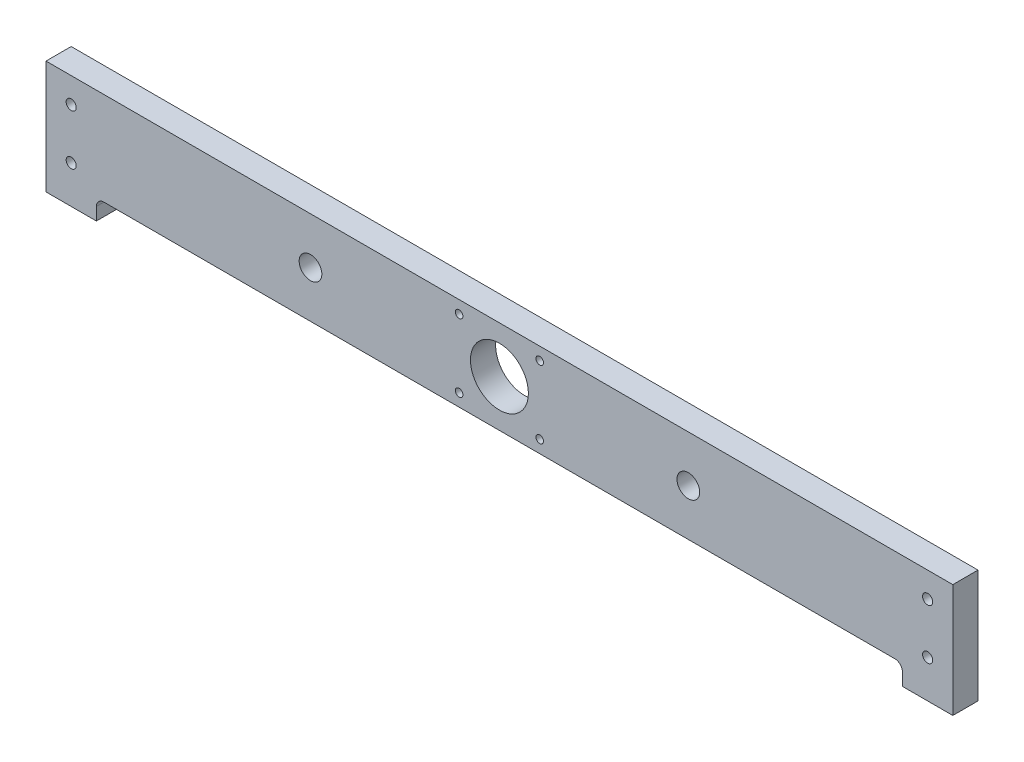
SolidWorks part; units mm, degrees
ref_plane "Front Plane" through (0, 0, 0) normal (0, 0, 1) x (1, 0, 0)
ref_plane "Top Plane" through (0, 0, 0) normal (0, 1, 0) x (1, 0, 0)
ref_plane "Right Plane" through (0, 0, 0) normal (1, 0, 0) x (0, 0, -1)
sketch "Sketch1" plane through (0, 0, 0) normal (0, 0, 1) x (1, 0, 0)
  line L0 (0, 0) -> (360, 0)
  line L1 (360, 0) -> (360, -45)
  line L2 (360, -45) -> (340, -45)
  line L3 (340, -45) -> (340, -40)
  line L4 (0, 0) -> (0, -45)
  line L5 (0, -45) -> (20, -45)
  line L6 (20, -45) -> (20, -40)
  line L7 (23, -37) -> (337, -37)
  arc A0 (23, -37) -> (20, -40) centre (23, -40) ccw
  arc A1 (340, -40) -> (337, -37) centre (337, -40) ccw
  circle A2 centre (350, -10) radius 2
  circle A3 centre (350, -30) radius 2
  circle A4 centre (10, -10) radius 2
  circle A5 centre (10, -30.0045) radius 2
  circle A6 centre (180, -18.5) radius 11.5
  circle A7 centre (255, -18.5) radius 4.5
  circle A8 centre (105, -18.5) radius 4.5
  circle A9 centre (164, -5) radius 1.5
  circle A10 centre (196, -5) radius 1.5
  circle A11 centre (196, -32) radius 1.5
  circle A12 centre (164, -32) radius 1.5
  point P11 (20, -37)
  point P29 (180, 0)
  point P37 (0, 0)
  point P38 (0, 0)
  dimension "D6" = 3
  dimension "D7" = 3
  dimension "D13" = 4
  dimension "D14" = 4
  dimension "D15" = 4
  dimension "D16" = 4
  dimension "D21" = 23
  dimension "D23" = 9
  dimension "D24" = 9
  dimension "D27" = 3
  dimension "D28" = 3
  dimension "D29" = 3
  dimension "D30" = 3
  dimension "D1" = 360
  dimension "D2" = 45
  dimension "D3" = 20
  dimension "D4" = 8
  dimension "D5" = 20
  dimension "D8" = 45
  dimension "D9" = 10
  dimension "D10" = 10
  dimension "D11" = 10
  dimension "D12" = 20
  dimension "D17" = 10
  dimension "D18" = 10
  dimension "D19" = 20.0045
  dimension "D20" = 10
  dimension "D22" = 18.5
  dimension "D25" = 75
  dimension "D26" = 75
  dimension "D31" = 5
  dimension "D32" = 5
  dimension "D33" = 32
  dimension "D34" = 32
  dimension "D35" = 5
  dimension "D36" = 16
extrude "Boss-Extrude1" add sketch "Sketch1" along normal blind 10
